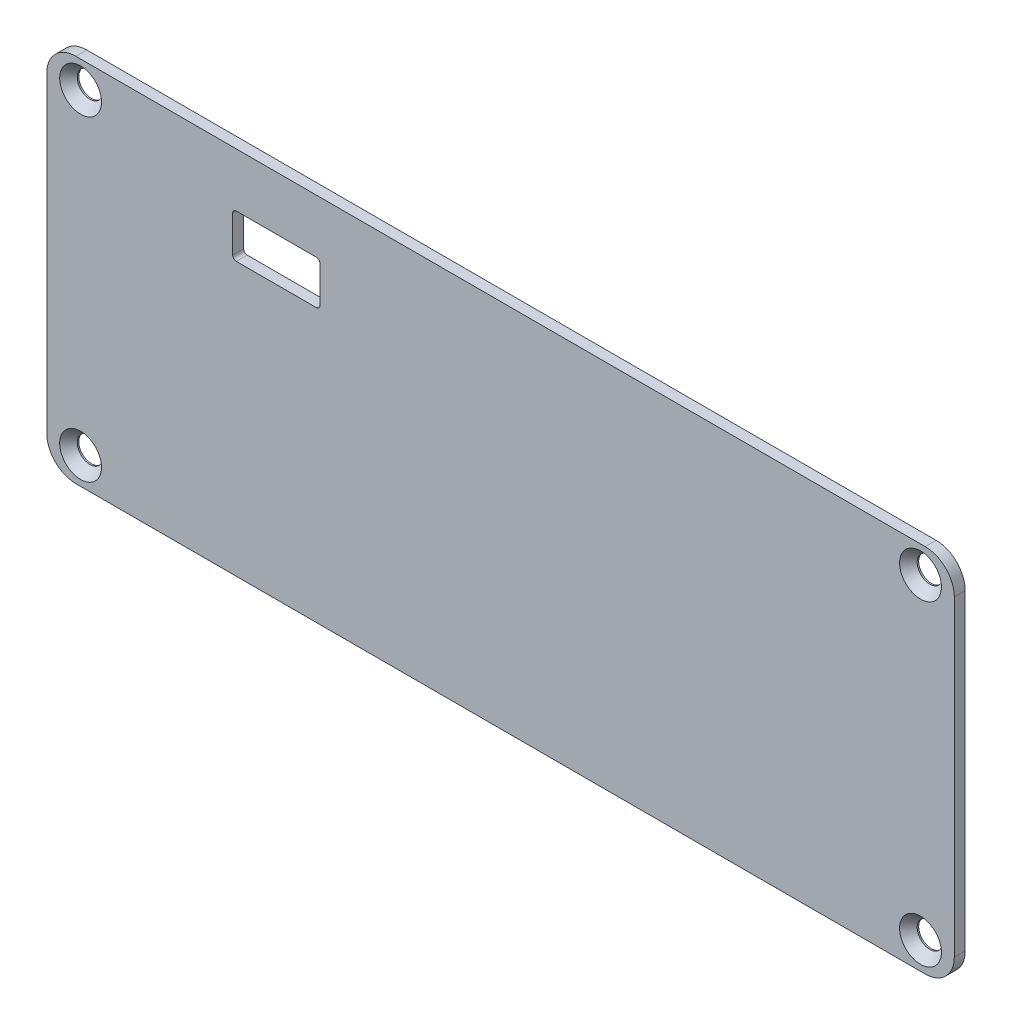
SolidWorks part; units mm, degrees
other "Markup1"
sketch "Sketch3" plane through (0, 0, 0) normal (-0.9973, 0.0561, -0.0476) x (-0.0483, -0.0106, 0.9988)
ref_plane "Front Plane" through (0, 0, 0) normal (0, 0, 1) x (1, 0, 0)
ref_plane "Top Plane" through (0, 0, 0) normal (0, 1, 0) x (1, 0, 0)
ref_plane "Right Plane" through (0, 0, 0) normal (1, 0, 0) x (0, 0, -1)
sketch "Sketch1" plane through (0, 0, 0) normal (0, 0, 1) x (1, 0, 0)
  line L1 (0, 0) -> (124.8, 0)
  line L2 (0, 0) -> (0, -50.9)
  line L3 (0, -50.9) -> (124.8, -50.9)
  line L4 (124.8, 0) -> (124.8, -50.9)
  line L17 (25.565, -7.4) -> (37.565, -7.4)
  line L18 (25.565, -7.4) -> (25.565, -13.4)
  line L19 (25.565, -13.4) -> (37.565, -13.4)
  line L20 (37.565, -7.4) -> (37.565, -13.4)
  point P5 (31.565, -10.4)
  point P7 (31.565, -7.4)
  point P8 (37.565, -10.4)
  dimension "D1" = 124.8
  dimension "D2" = 50.9
  dimension "D3" = 31.565
  dimension "D4" = 10.4
  dimension "D5" = 31.565
  dimension "D6" = 10.4
  dimension "D7" = 12
  dimension "D8" = 6
extrude "Boss-Extrude1" add sketch "Sketch1" along normal blind 1.5
hole_wizard "CSK for M3.5 Flat Head Machine Screw1" positions "3DSketch1" profile "Sketch2" countersink size "M3.5" standard "ANSI Metric" end condition through all
sketch3d "3DSketch1"
  line L3 (0, 0, 1.5) -> (124.8, 0, 1.5) construction
  line L4 (124.8, 0, 1.5) -> (124.8, -50.9, 1.5) construction
  point P0 (4.65, -3.7, 1.5)
  point P2 (120.15, -3.7, 1.5)
  point P4 (120.15, -47.2, 1.5)
  point P6 (4.65, -47.2, 1.5)
  dimension "D1" = 115.5
  dimension "D2" = 43.5
  dimension "D3" = 3.7
  dimension "D4" = 4.65
sketch "Sketch2" plane through (4.65, -3.7, 1.5) normal (1, 0, 0) x (0, -1, 0)
  line L0 (0, 0) -> (0, 1.5)
  line L1 (0, 1.5) -> (1.75, 1.5)
  line L2 (1.75, 1.5) -> (1.75, 1.2942)
  line L3 (1.75, 1.2942) -> (2.875, 0)
  line L5 (2.875, 0) -> (0, 0)
  line L6 (-1.75, 1.2942) -> (-2.875, 0) construction
  line L11 (0, -6.35) -> (0, 107.95) construction
  dimension "Thru Hole Dia." = 3.5
  dimension "Thru Hole Depth" = 1.5
  dimension "Near C'Sink Dia." = 5.75
  dimension "Near C'Sink Angle" = 82
fillet "Fillet2" radius 4 4 edges at (0, 0, 0.75) (124.8, 0, 0.75) (124.8, -50.9, 0.75) (0, -50.9, 0.75)
fillet "Fillet3" radius 0.5 4 edges at (25.565, -13.4, 0.75) (37.565, -13.4, 0.75) (37.565, -7.4, 0.75) (25.565, -7.4, 0.75)
